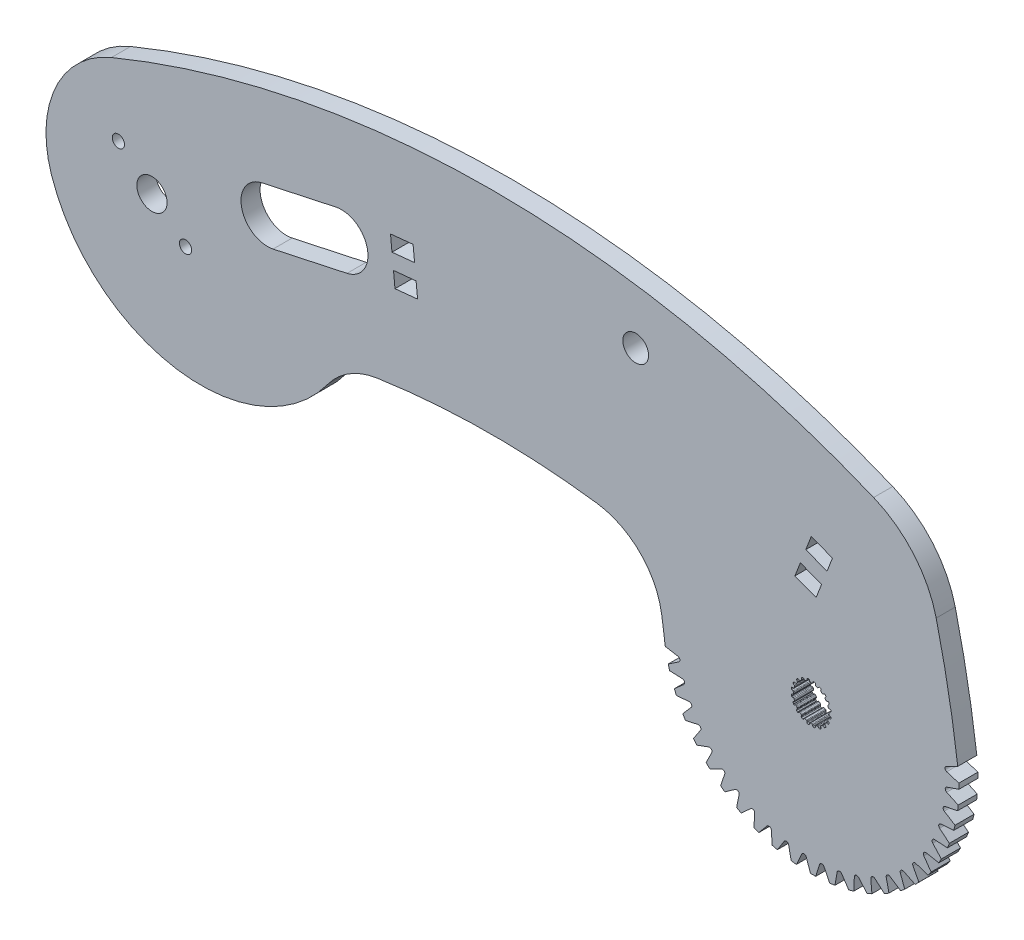
SolidWorks part; units mm, degrees
ref_plane "Front Plane" through (0, 0, 0) normal (0, 0, 1) x (1, 0, 0)
ref_plane "Top Plane" through (0, 0, 0) normal (0, 1, 0) x (1, 0, 0)
ref_plane "Right Plane" through (0, 0, 0) normal (1, 0, 0) x (0, 0, -1)
sketch "Sketch1" plane through (0, 0, 0) normal (0, 0, 1) x (1, 0, 0)
  line L84 (-6.7901, 16.4357) -> (6.7901, -16.4357) construction
  line L85 (121.0901, 16.4357) -> (107.5099, -16.4357) construction
  line L86 (0, 0) -> (114.3, 0) construction
  arc A81 (-6.7901, 16.4357) -> (121.0901, 16.4357) centre (57.15, -138.3341) cw
  arc A82 (6.7901, -16.4357) -> (107.5099, -16.4357) centre (57.15, -138.3341) cw
  arc A84 (-6.7901, 16.4357) -> (6.7901, -16.4357) centre (0, 0) ccw
  arc A85 (121.0901, 16.4357) -> (107.5099, -16.4357) centre (114.3, 0) cw
  dimension "D10" = 131.8914
  dimension "D11" = 35.5662
  dimension "D12" = 114.3
extrude "Boss-Extrude1" add sketch "Sketch1" along normal blind 3.2004
sketch "Sketch3" plane through (0, 0, 3.2004) normal (0, 0, 1) x (1, 0, 0)
  line L0 (114.3, 0) -> (110.6075, -18.6887) construction
  line L5 (83.3792, -7.4554) -> (131.5877, 4.1683)
  line L6 (0, 0) -> (114.3, 0) construction
  line L7 (86.0089, -21.8032) -> (135.2061, -15.5742) construction
  arc A1 (107.5099, -16.4357) -> (121.0901, 16.4357) centre (114.3, 0) ccw construction
  arc A2 (86.0089, -21.8032) -> (135.2061, -15.5742) centre (110.6075, -18.6887) ccw
  arc A3 (83.3792, -7.4554) -> (86.0089, -21.8032) centre (-44.8379, -38.37) cw
  arc A4 (131.5877, 4.1683) -> (135.2061, -15.5742) centre (-44.8379, -38.37) cw
  dimension "D1" = 131.8914
  dimension "D2" = 19.05
  dimension "D3" = 78.823
  dimension "D4" = 49.59
extrude "Boss-Extrude2" add sketch "Sketch3" against normal up to surface (3.2004 mm away) up to face at (57.15, 2.2751, 0)
sketch "Sketch4" plane through (0, 0, 3.2004) normal (0, 0, 1) x (1, 0, 0)
  line L0 (110.5005, -15.7188) -> (110.7144, -15.7188)
  line L1 (110.9234, -15.4512) -> (110.8612, -15.6312)
  line L2 (110.3111, -15.4521) -> (110.3757, -15.6312)
  line L3 (110.3111, -15.4521) -> (110.9234, -15.4512) construction
  line L4 (110.6075, -15.3635) -> (110.6075, -18.6887) construction
  line L5 (110.3757, -15.6312) -> (110.8612, -15.6312) construction
  line L6 (110.1793, -15.3646) -> (111.0356, -15.3624) construction
  line L7 (111.3258, -15.5189) -> (111.3319, -15.7092)
  line L8 (111.4235, -15.8311) -> (111.6269, -15.8972)
  line L9 (111.9084, -15.7073) -> (111.7936, -15.8592)
  line L10 (112.2701, -15.896) -> (112.2171, -16.0789)
  line L11 (112.2666, -16.2232) -> (112.4397, -16.3489)
  line L12 (112.766, -16.2552) -> (112.6099, -16.3642)
  line L13 (113.0518, -16.5464) -> (112.9448, -16.704)
  line L14 (112.9473, -16.8565) -> (113.073, -17.0296)
  line L15 (113.4124, -17.0413) -> (113.2302, -17.0968)
  line L16 (113.5941, -17.4066) -> (113.4438, -17.5234)
  line L17 (113.3989, -17.6693) -> (113.465, -17.8727)
  line L18 (113.7842, -17.9887) -> (113.5938, -17.9852)
  line L19 (113.8441, -18.3923) -> (113.665, -18.4569)
  line L20 (113.5774, -18.5818) -> (113.5774, -18.7957)
  line L21 (113.845, -19.0046) -> (113.665, -18.9424)
  line L22 (113.7773, -19.407) -> (113.587, -19.4131)
  line L23 (113.465, -19.5047) -> (113.3989, -19.7082)
  line L24 (113.5889, -19.9896) -> (113.437, -19.8749)
  line L25 (113.4002, -20.3514) -> (113.2173, -20.2984)
  line L26 (113.073, -20.3478) -> (112.9473, -20.5209)
  line L27 (113.041, -20.8472) -> (112.9319, -20.6912)
  line L28 (112.7497, -21.133) -> (112.5922, -21.0261)
  line L29 (112.4397, -21.0285) -> (112.2666, -21.1543)
  line L30 (112.2549, -21.4936) -> (112.1994, -21.3115)
  line L31 (111.8896, -21.6753) -> (111.7728, -21.525)
  line L32 (111.6269, -21.4802) -> (111.4235, -21.5463)
  line L33 (111.3075, -21.8654) -> (111.311, -21.675)
  line L34 (110.9039, -21.9254) -> (110.8393, -21.7463)
  line L35 (110.7144, -21.6586) -> (110.5005, -21.6586)
  line L36 (110.2916, -21.9262) -> (110.3537, -21.7463)
  line L37 (109.8892, -21.8585) -> (109.8831, -21.6682)
  line L38 (109.7915, -21.5463) -> (109.588, -21.4802)
  line L39 (109.3066, -21.6702) -> (109.4213, -21.5182)
  line L40 (108.9448, -21.4814) -> (108.9978, -21.2986)
  line L41 (108.9484, -21.1543) -> (108.7753, -21.0285)
  line L42 (108.4489, -21.1222) -> (108.605, -21.0132)
  line L43 (108.1632, -20.831) -> (108.2701, -20.6734)
  line L44 (108.2677, -20.5209) -> (108.1419, -20.3478)
  line L45 (107.8026, -20.3361) -> (107.9847, -20.2806)
  line L46 (107.6208, -19.9708) -> (107.7712, -19.854)
  line L47 (107.816, -19.7082) -> (107.7499, -19.5047)
  line L48 (107.4308, -19.3887) -> (107.6212, -19.3922)
  line L49 (107.3708, -18.9851) -> (107.5499, -18.9205)
  line L50 (107.6376, -18.7957) -> (107.6376, -18.5818)
  line L51 (107.37, -18.3728) -> (107.5499, -18.435)
  line L52 (107.4376, -17.9704) -> (107.628, -17.9643)
  line L53 (107.7499, -17.8727) -> (107.816, -17.6693)
  line L54 (107.626, -17.3878) -> (107.778, -17.5026)
  line L55 (107.8147, -17.0261) -> (107.9976, -17.079)
  line L56 (108.1419, -17.0296) -> (108.2677, -16.8565)
  line L57 (108.1739, -16.5302) -> (108.283, -16.6862)
  line L58 (108.4652, -16.2444) -> (108.6228, -16.3513)
  line L59 (108.7753, -16.3489) -> (108.9484, -16.2232)
  line L60 (108.9601, -15.8838) -> (109.0156, -16.066)
  line L61 (109.3254, -15.7021) -> (109.4422, -15.8524)
  line L62 (109.588, -15.8972) -> (109.7915, -15.8311)
  line L63 (109.9075, -15.512) -> (109.904, -15.7024)
  line L64 (111.0356, -15.3624) -> (111.2275, -15.395)
  line L65 (112.0425, -15.6575) -> (112.215, -15.7478)
  line L66 (112.909, -16.2494) -> (113.0451, -16.3884)
  line L67 (113.5501, -17.08) -> (113.6366, -17.2543)
  line L68 (113.9033, -18.068) -> (113.9316, -18.2606)
  line L69 (113.9337, -19.1169) -> (113.9012, -19.3087)
  line L70 (113.6386, -20.1238) -> (113.5484, -20.2962)
  line L71 (113.0468, -20.9902) -> (112.9077, -21.1263)
  line L72 (112.2162, -21.6314) -> (112.0419, -21.7179)
  line L73 (111.2282, -21.9845) -> (111.0356, -22.0129)
  line L74 (110.1793, -22.015) -> (109.9875, -21.9825)
  line L75 (109.1724, -21.7199) -> (109, -21.6297)
  line L76 (108.306, -21.1281) -> (108.1698, -20.989)
  line L77 (107.6648, -20.2975) -> (107.5783, -20.1231)
  line L78 (107.3117, -19.3094) -> (107.2833, -19.1169)
  line L79 (107.2812, -18.2606) -> (107.3137, -18.0687)
  line L80 (107.5763, -17.2536) -> (107.6665, -17.0812)
  line L81 (108.1681, -16.3872) -> (108.3072, -16.2511)
  line L82 (108.9987, -15.746) -> (109.1731, -15.6596)
  line L83 (109.9868, -15.3929) -> (110.1793, -15.3646)
  circle A0 centre (0, 0) radius 2.54
  circle A1 centre (110.6075, -18.6887) radius 3.429 construction
  arc A2 (86.0089, -21.8032) -> (135.2061, -15.5742) centre (110.6075, -18.6887) ccw construction
  arc A3 (-6.7901, 16.4357) -> (6.7901, -16.4357) centre (0, 0) ccw construction
  arc A4 (110.8612, -15.6312) -> (110.7144, -15.7188) centre (110.7358, -15.5878) cw
  arc A5 (110.3757, -15.6312) -> (110.5005, -15.7188) centre (110.5005, -15.5861) ccw
  arc A6 (111.2275, -15.395) -> (111.3258, -15.5189) centre (111.1931, -15.5231) cw
  arc A7 (111.3319, -15.7092) -> (111.4235, -15.8311) centre (111.4645, -15.7049) ccw
  arc A8 (110.1793, -15.3646) -> (110.3111, -15.4521) centre (110.1862, -15.4971) cw
  arc A9 (111.0356, -15.3624) -> (110.9234, -15.4512) centre (111.0488, -15.4945) ccw
  arc A10 (111.7936, -15.8592) -> (111.6269, -15.8972) centre (111.6877, -15.7793) cw
  arc A11 (112.0425, -15.6575) -> (111.9084, -15.7073) centre (112.0143, -15.7872) ccw
  arc A12 (112.215, -15.7478) -> (112.2701, -15.896) centre (112.1427, -15.859) cw
  arc A13 (112.2171, -16.0789) -> (112.2666, -16.2232) centre (112.3446, -16.1158) ccw
  arc A14 (112.6099, -16.3642) -> (112.4397, -16.3489) centre (112.5339, -16.2555) cw
  arc A15 (112.909, -16.2494) -> (112.766, -16.2552) centre (112.842, -16.364) ccw
  arc A16 (113.0451, -16.3884) -> (113.0518, -16.5464) centre (112.9419, -16.4719) cw
  arc A17 (112.9448, -16.704) -> (112.9473, -16.8565) centre (113.0547, -16.7785) ccw
  arc A18 (113.2302, -17.0968) -> (113.073, -17.0296) centre (113.1915, -16.9699) cw
  arc A19 (113.5501, -17.08) -> (113.4124, -17.0413) centre (113.4511, -17.1682) ccw
  arc A20 (113.6366, -17.2543) -> (113.5941, -17.4066) centre (113.5127, -17.3018) cw
  arc A21 (113.4438, -17.5234) -> (113.3989, -17.6693) centre (113.5252, -17.6282) ccw
  arc A22 (113.5938, -17.9852) -> (113.465, -17.8727) centre (113.5962, -17.8525) cw
  arc A23 (113.9033, -18.068) -> (113.7842, -17.9887) centre (113.7817, -18.1214) ccw
  arc A24 (113.9316, -18.2606) -> (113.8441, -18.3923) centre (113.7991, -18.2675) cw
  arc A25 (113.665, -18.4569) -> (113.5774, -18.5818) centre (113.7101, -18.5818) ccw
  arc A26 (113.665, -18.9424) -> (113.5774, -18.7957) centre (113.7083, -18.817) cw
  arc A27 (113.9337, -19.1169) -> (113.845, -19.0046) centre (113.8017, -19.13) ccw
  arc A28 (113.9012, -19.3087) -> (113.7773, -19.407) centre (113.7731, -19.2743) cw
  arc A29 (113.587, -19.4131) -> (113.465, -19.5047) centre (113.5913, -19.5457) ccw
  arc A30 (113.437, -19.8749) -> (113.3989, -19.7082) centre (113.5169, -19.7689) cw
  arc A31 (113.6386, -20.1238) -> (113.5889, -19.9896) centre (113.509, -20.0955) ccw
  arc A32 (113.5484, -20.2962) -> (113.4002, -20.3514) centre (113.4372, -20.2239) cw
  arc A33 (113.2173, -20.2984) -> (113.073, -20.3478) centre (113.1804, -20.4258) ccw
  arc A34 (112.9319, -20.6912) -> (112.9473, -20.5209) centre (113.0407, -20.6151) cw
  arc A35 (113.0468, -20.9902) -> (113.041, -20.8472) centre (112.9322, -20.9233) ccw
  arc A36 (112.9077, -21.1263) -> (112.7497, -21.133) centre (112.8243, -21.0232) cw
  arc A37 (112.5922, -21.0261) -> (112.4397, -21.0285) centre (112.5177, -21.1359) ccw
  arc A38 (112.1994, -21.3115) -> (112.2666, -21.1543) centre (112.3263, -21.2728) cw
  arc A39 (112.2162, -21.6314) -> (112.2549, -21.4936) centre (112.1279, -21.5323) ccw
  arc A40 (112.0419, -21.7179) -> (111.8896, -21.6753) centre (111.9944, -21.5939) cw
  arc A41 (111.7728, -21.525) -> (111.6269, -21.4802) centre (111.6679, -21.6064) ccw
  arc A42 (111.311, -21.675) -> (111.4235, -21.5463) centre (111.4437, -21.6775) cw
  arc A43 (111.2282, -21.9845) -> (111.3075, -21.8654) centre (111.1748, -21.863) ccw
  arc A44 (111.0356, -22.0129) -> (110.9039, -21.9254) centre (111.0287, -21.8803) cw
  arc A45 (110.8393, -21.7463) -> (110.7144, -21.6586) centre (110.7144, -21.7913) ccw
  arc A46 (110.3537, -21.7463) -> (110.5005, -21.6586) centre (110.4792, -21.7896) cw
  arc A47 (110.1793, -22.015) -> (110.2916, -21.9262) centre (110.1661, -21.8829) ccw
  arc A48 (109.9875, -21.9825) -> (109.8892, -21.8585) centre (110.0219, -21.8543) cw
  arc A49 (109.8831, -21.6682) -> (109.7915, -21.5463) centre (109.7504, -21.6725) ccw
  arc A50 (109.4213, -21.5182) -> (109.588, -21.4802) centre (109.5272, -21.5982) cw
  arc A51 (109.1724, -21.7199) -> (109.3066, -21.6702) centre (109.2007, -21.5902) ccw
  arc A52 (109, -21.6297) -> (108.9448, -21.4814) centre (109.0723, -21.5184) cw
  arc A53 (108.9978, -21.2986) -> (108.9484, -21.1543) centre (108.8703, -21.2616) ccw
  arc A54 (108.605, -21.0132) -> (108.7753, -21.0285) centre (108.681, -21.122) cw
  arc A55 (108.306, -21.1281) -> (108.4489, -21.1222) centre (108.3729, -21.0135) ccw
  arc A56 (108.1698, -20.989) -> (108.1632, -20.831) centre (108.273, -20.9055) cw
  arc A57 (108.2701, -20.6734) -> (108.2677, -20.5209) centre (108.1603, -20.5989) ccw
  arc A58 (107.9847, -20.2806) -> (108.1419, -20.3478) centre (108.0234, -20.4076) cw
  arc A59 (107.6648, -20.2975) -> (107.8026, -20.3361) centre (107.7639, -20.2092) ccw
  arc A60 (107.5783, -20.1231) -> (107.6208, -19.9708) centre (107.7023, -20.0756) cw
  arc A61 (107.7712, -19.854) -> (107.816, -19.7082) centre (107.6898, -19.7492) ccw
  arc A62 (107.6212, -19.3922) -> (107.7499, -19.5047) centre (107.6187, -19.5249) cw
  arc A63 (107.3117, -19.3094) -> (107.4308, -19.3887) centre (107.4332, -19.256) ccw
  arc A64 (107.2833, -19.1169) -> (107.3708, -18.9851) centre (107.4159, -19.11) cw
  arc A65 (107.5499, -18.9205) -> (107.6376, -18.7957) centre (107.5049, -18.7957) ccw
  arc A66 (107.5499, -18.435) -> (107.6376, -18.5818) centre (107.5066, -18.5604) cw
  arc A67 (107.2812, -18.2606) -> (107.37, -18.3728) centre (107.4133, -18.2474) ccw
  arc A68 (107.3137, -18.0687) -> (107.4376, -17.9704) centre (107.4419, -18.1031) cw
  arc A69 (107.628, -17.9643) -> (107.7499, -17.8727) centre (107.6237, -17.8317) ccw
  arc A70 (107.778, -17.5026) -> (107.816, -17.6693) centre (107.698, -17.6085) cw
  arc A71 (107.5763, -17.2536) -> (107.626, -17.3878) centre (107.706, -17.2819) ccw
  arc A72 (107.6665, -17.0812) -> (107.8147, -17.0261) centre (107.7778, -17.1535) cw
  arc A73 (107.9976, -17.079) -> (108.1419, -17.0296) centre (108.0346, -16.9516) ccw
  arc A74 (108.283, -16.6862) -> (108.2677, -16.8565) centre (108.1742, -16.7623) cw
  arc A75 (108.1681, -16.3872) -> (108.1739, -16.5302) centre (108.2827, -16.4541) ccw
  arc A76 (108.3072, -16.2511) -> (108.4652, -16.2444) centre (108.3907, -16.3543) cw
  arc A77 (108.6228, -16.3513) -> (108.7753, -16.3489) centre (108.6973, -16.2415) ccw
  arc A78 (109.0156, -16.066) -> (108.9484, -16.2232) centre (108.8886, -16.1046) cw
  arc A79 (108.9987, -15.746) -> (108.9601, -15.8838) centre (109.087, -15.8451) ccw
  arc A80 (109.1731, -15.6596) -> (109.3254, -15.7021) centre (109.2206, -15.7835) cw
  arc A81 (109.4422, -15.8524) -> (109.588, -15.8972) centre (109.547, -15.771) ccw
  arc A82 (109.904, -15.7024) -> (109.7915, -15.8311) centre (109.7713, -15.7) cw
  arc A83 (109.9868, -15.3929) -> (109.9075, -15.512) centre (110.0402, -15.5145) ccw
  circle A84 centre (110.6075, -18.6887) radius 12.7 construction
  point P24 (110.6075, -15.7188)
  dimension "D1" = 6.858
  dimension "D2" = 5.08
  dimension "D5" = 0.1327
  dimension "D10" = 25.4
  dimension "D3" = 0.2139
  dimension "D4" = 0.1904
  dimension "D6" = 0.4855
  dimension "D7" = 0.0877
  dimension "D8" = 0.8563
  dimension "D9" = 2.9699
extrude "Cut-Extrude1" cut sketch "Sketch4" against normal up to surface (3.2004 mm away) up to face at (77.9577, -5.3609, 0)
fillet "Fillet1" radius 12.7 1 edges at (83.7779, -9.1587, 1.6002)
sketch "Sketch7" plane through (0, 0, 3.2004) normal (0, 0, 1) x (1, 0, 0)
  circle A0 centre (110.6075, -18.6887) radius 23.8032 construction
  circle A2 centre (110.6075, -18.6887) radius 12.7 construction
  dimension "D1" = 47.6064
sketch "Sketch8" plane through (0, 0, 3.2004) normal (0, 0, 1) x (1, 0, 0)
  line L0 (-5.6385, 4.8574) -> (5.6385, -4.8574) construction
  line L1 (-6.7901, 16.4357) -> (6.7901, -16.4357) construction
  circle A0 centre (-5.6385, 4.8574) radius 1.025
  circle A1 centre (5.6385, -4.8574) radius 1.025
  circle A4 centre (0, 0) radius 2.54 construction
  point P10 (0, 0)
  dimension "D1" = 2.05
  dimension "D2" = 14.8844
  dimension "D3" = 26.809
extrude "Cut-Extrude3" cut sketch "Sketch8" against normal up to surface (3.2004 mm away) up to face at (77.9593, -6.7182, 0)
sketch "Sketch9" plane through (0, 0, 0) normal (0, 0, -1) x (-1, 0, 0)
  line L0 (-42.0442, 13.129) -> (-42.5483, 8.074) construction
  line L1 (-32.7374, 4.833) -> (-20.3234, 2.1529)
  line L2 (-32.7374, 4.833) -> (-30.8613, 13.5228) construction
  line L3 (-30.8613, 13.5228) -> (-18.4473, 10.8427)
  line L4 (-20.3234, 2.1529) -> (-18.4473, 10.8427) construction
  line L5 (-26.5304, 3.4929) -> (-24.6543, 12.1827) construction
  line L6 (-121.0901, 16.4357) -> (-107.5099, -16.4357) construction
  line L7 (6.7901, 16.4357) -> (-6.7901, -16.4357) construction
  line L8 (-111.9474, 3.6747) -> (-110.1186, -1.0647) construction
  line L9 (-40.4007, 10.4124) -> (-44.1919, 10.7906) construction
  line L10 (-112.8103, 0.6192) -> (-109.2557, 1.9908) construction
  line L11 (-43.9398, 13.318) -> (-40.1486, 12.9399) construction
  line L12 (-43.8138, 14.5817) -> (-40.0226, 14.2036)
  line L13 (-43.8138, 14.5817) -> (-44.0658, 12.0543)
  line L14 (-44.0658, 12.0543) -> (-40.2746, 11.6762)
  line L15 (-40.0226, 14.2036) -> (-40.2746, 11.6762)
  line L20 (-44.4439, 8.2631) -> (-40.6528, 7.885) construction
  line L21 (-44.3179, 9.5268) -> (-40.5267, 9.1487)
  line L22 (-44.3179, 9.5268) -> (-44.57, 6.9994)
  line L23 (-44.57, 6.9994) -> (-40.7788, 6.6213)
  line L24 (-40.5267, 9.1487) -> (-40.7788, 6.6213)
  line L25 (-113.7247, 2.9889) -> (-110.1701, 4.3605) construction
  line L26 (-114.1819, 4.1737) -> (-110.6273, 5.5453)
  line L27 (-114.1819, 4.1737) -> (-113.2675, 1.804)
  line L28 (-113.2675, 1.804) -> (-109.7129, 3.1756)
  line L29 (-110.6273, 5.5453) -> (-109.7129, 3.1756)
  line L30 (-111.8959, -1.7505) -> (-108.3413, -0.3789) construction
  line L31 (-112.3531, -0.5657) -> (-108.7985, 0.8059)
  line L32 (-112.3531, -0.5657) -> (-111.4386, -2.9354)
  line L33 (-111.4386, -2.9354) -> (-107.8841, -1.5638)
  line L34 (-108.7985, 0.8059) -> (-107.8841, -1.5638)
  circle A0 centre (0, 0) radius 2.54 construction
  arc A1 (-114.3, 0) -> (0, 0) centre (-57.15, -138.3341) cw construction
  arc A2 (6.7901, 16.4357) -> (-121.0901, 16.4357) centre (-57.15, -138.3341) ccw construction
  arc A3 (-30.8613, 13.5228) -> (-32.7374, 4.833) centre (-31.7993, 9.1779) ccw
  arc A4 (-18.4473, 10.8427) -> (-20.3234, 2.1529) centre (-19.3853, 6.4978) cw
  point P19 (-31.7993, 9.1779)
  point P20 (-19.3853, 6.4978)
  point P26 (-111.033, 1.305)
  point P27 (-42.2963, 10.6015)
  dimension "D1" = 8.89
  dimension "D2" = 12.7
  dimension "D3" = 20.32
  dimension "D4" = 3.81
  dimension "D5" = 2.54
  dimension "D6" = 3.81
  dimension "D7" = 5.08
extrude "Cut-Extrude4" cut sketch "Sketch9" against normal up to surface (3.2004 mm away) up to face at (-4.6135, 4.8574, 3.2004)
sketch "Sketch10" plane through (0, 0, 0) normal (0, 0, -1) x (-1, 0, 0)
  line L0 (-37.8089, -7.8686) -> (16.8684, -5.63)
  line L1 (0, 0) -> (-114.3, 0) construction
  arc A0 (-37.8089, -7.8686) -> (-29.5382, -12.8633) centre (-39.6449, -20.2538) cw
  arc A1 (-29.5382, -12.8633) -> (16.8684, -5.63) centre (-8.2029, 2.7378) ccw
  arc A2 (-6.7901, -16.4357) -> (-74.6443, -7.6081) centre (-57.15, -138.3341) ccw construction
  arc A3 (-6.7901, -16.4357) -> (6.7901, 16.4357) centre (0, 0) ccw construction
  dimension "D1" = 54.723
  dimension "D2" = 9.6619
  dimension "D3" = 7.8686
extrude "Boss-Extrude3" add sketch "Sketch10" against normal up to surface (3.2004 mm away) up to face at (25.5923, 7.8378, 3.2004)
sketch "Sketch15" plane through (0, 0, 3.2004) normal (0, 0, 1) x (1, 0, 0)
  line L0 (110.6075, -18.6887) -> (135.2983, -16.7468) construction
  line L1 (135.2061, -15.5742) -> (133.2934, -16.5226)
  line L2 (135.3905, -17.9195) -> (133.3531, -17.2818)
  line L3 (135.2061, -15.5742) -> (135.3905, -17.9195) construction
  line L4 (134.2497, -16.0484) -> (134.3718, -17.6006) construction
  line L5 (158.1361, -16.5125) -> (110.6075, -18.6887) construction
  line L6 (135.4022, -18.8116) -> (133.382, -19.5022)
  line L7 (135.2789, -21.1609) -> (133.3421, -20.2627)
  line L8 (135.174, -22.0469) -> (133.081, -22.4679)
  line L9 (134.7452, -24.36) -> (132.9422, -23.2167)
  line L10 (134.5255, -25.2248) -> (132.3955, -25.369)
  line L11 (133.7984, -27.4621) -> (132.1601, -26.0933)
  line L12 (133.4677, -28.2908) -> (131.3371, -28.1557)
  line L13 (132.4549, -30.414) -> (131.0092, -28.8431)
  line L14 (132.0189, -31.1925) -> (129.9241, -30.7805)
  line L15 (130.7375, -33.1654) -> (129.5093, -31.4192)
  line L16 (130.2036, -33.8803) -> (128.1805, -33.1984)
  line L17 (128.6757, -35.669) -> (127.6859, -33.7774)
  line L18 (128.0531, -36.3081) -> (126.1363, -35.368)
  line L19 (126.3047, -37.8821) -> (125.5703, -35.8775)
  line L20 (125.604, -38.4345) -> (123.8264, -37.2522)
  line L21 (123.6652, -39.7668) -> (123.1987, -37.6835)
  line L22 (122.8984, -40.223) -> (121.2902, -38.8188)
  line L23 (120.8022, -41.2909) -> (120.6117, -39.1645)
  line L24 (119.9824, -41.6431) -> (118.5714, -40.041)
  line L25 (117.7648, -42.4282) -> (117.8534, -40.2951)
  line L26 (116.9061, -42.6704) -> (115.7162, -40.8978)
  line L27 (114.605, -43.1593) -> (114.9713, -41.0561)
  line L28 (113.722, -43.2873) -> (112.7736, -41.3746)
  line L29 (111.3767, -43.4718) -> (112.0144, -41.4343)
  line L30 (110.4845, -43.4834) -> (109.794, -41.4633)
  line L31 (108.1353, -43.3602) -> (109.0335, -41.4234)
  line L32 (107.2492, -43.2552) -> (106.8283, -41.1622)
  line L33 (104.9362, -42.8264) -> (106.0795, -41.0234)
  line L34 (104.0714, -42.6067) -> (103.9272, -40.4767)
  line L35 (101.8341, -41.8797) -> (103.2029, -40.2413)
  line L36 (101.0054, -41.549) -> (101.1405, -39.4183)
  line L37 (98.8821, -40.5361) -> (100.4531, -39.0904)
  line L38 (98.1037, -40.1001) -> (98.5157, -38.0053)
  line L39 (96.1308, -38.8187) -> (97.877, -37.5905)
  line L40 (95.4159, -38.2848) -> (96.0978, -36.2617)
  line L41 (93.6271, -36.7569) -> (95.5188, -35.7671)
  line L42 (92.9881, -36.1343) -> (93.9282, -34.2175)
  line L43 (91.414, -34.386) -> (93.4187, -33.6515)
  line L44 (90.8617, -33.6852) -> (92.044, -31.9076)
  line L45 (89.5293, -31.7464) -> (91.6127, -31.2799)
  line L46 (89.0732, -30.9796) -> (90.4774, -29.3715)
  line L47 (88.0053, -28.8835) -> (90.1317, -28.6929)
  line L48 (87.6531, -28.0637) -> (89.2552, -26.6526)
  line L49 (86.868, -25.8461) -> (89.0011, -25.9347)
  line L50 (86.6258, -24.9873) -> (88.3984, -23.7974)
  line L51 (86.1368, -22.6862) -> (88.2401, -23.0525)
  line L52 (86.0089, -21.8032) -> (87.9216, -20.8549) construction
  line L53 (85.8244, -19.458) -> (87.8619, -20.0956) construction
  line L54 (85.8128, -18.5658) -> (87.8329, -17.8752) construction
  line L55 (85.936, -16.2165) -> (87.8728, -17.1147) construction
  line L56 (86.0409, -15.3305) -> (88.134, -14.9095) construction
  line L57 (86.4698, -13.0174) -> (88.2728, -14.1607) construction
  line L58 (86.6895, -12.1526) -> (88.8195, -12.0084) construction
  line L59 (87.4165, -9.9153) -> (89.0549, -11.2842) construction
  line L60 (87.7472, -9.0866) -> (89.8779, -9.2217) construction
  line L61 (88.7601, -6.9634) -> (90.2058, -8.5343) construction
  line L62 (89.1961, -6.1849) -> (91.2909, -6.5969) construction
  line L63 (90.4775, -4.212) -> (91.7057, -5.9582) construction
  line L64 (91.0114, -3.4971) -> (93.0344, -4.1791) construction
  line L65 (92.5393, -1.7084) -> (93.5291, -3.6) construction
  line L66 (93.1619, -1.0693) -> (95.0787, -2.0094) construction
  line L67 (94.9102, 0.5047) -> (95.6447, -1.4999) construction
  line L68 (95.611, 1.0571) -> (97.3886, -0.1252) construction
  line L69 (97.5498, 2.3894) -> (98.0163, 0.3061) construction
  line L70 (98.3166, 2.8456) -> (99.9247, 1.4414) construction
  line L71 (100.4127, 3.9135) -> (100.6033, 1.7871) construction
  line L72 (101.2325, 4.2656) -> (102.6436, 2.6635) construction
  line L73 (103.4501, 5.0508) -> (103.3615, 2.9177) construction
  line L74 (104.3089, 5.2929) -> (105.4988, 3.5204) construction
  line L75 (106.61, 5.7819) -> (106.2437, 3.6787) construction
  line L76 (107.493, 5.9099) -> (108.4413, 3.9972) construction
  line L77 (109.8382, 6.0944) -> (109.2006, 4.0569) construction
  line L78 (110.7304, 6.106) -> (111.421, 4.0858) construction
  line L79 (113.0796, 5.9827) -> (112.1815, 4.0459) construction
  line L80 (113.9657, 5.8778) -> (114.3867, 3.7848) construction
  line L81 (116.2788, 5.449) -> (115.1355, 3.646) construction
  line L82 (117.1436, 5.2293) -> (117.2877, 3.0993) construction
  line L83 (119.3809, 4.5022) -> (118.012, 2.8639) construction
  line L84 (120.2096, 4.1716) -> (120.0745, 2.0409) construction
  line L85 (122.3328, 3.1587) -> (120.7619, 1.713) construction
  line L86 (123.1113, 2.7227) -> (122.6993, 0.6279) construction
  line L87 (125.0842, 1.4413) -> (123.3379, 0.2131) construction
  line L88 (125.7991, 0.9074) -> (125.1171, -1.1157) construction
  line L89 (127.5878, -0.6205) -> (125.6962, -1.6103) construction
  line L90 (128.2269, -1.2431) -> (127.2867, -3.1599) construction
  line L91 (129.8009, -2.9914) -> (127.7963, -3.7259) construction
  line L92 (130.3533, -3.6922) -> (129.171, -5.4698) construction
  line L93 (131.6856, -5.631) -> (129.6023, -6.0975) construction
  line L94 (132.1418, -6.3978) -> (130.7376, -8.0059) construction
  line L95 (133.2097, -8.4939) -> (131.0833, -8.6845) construction
  line L96 (133.5618, -9.3138) -> (131.9597, -10.7248) construction
  line L97 (134.347, -11.5313) -> (132.2139, -11.4427) construction
  line L98 (134.5891, -12.3901) -> (132.8165, -13.58) construction
  line L99 (135.0781, -14.6912) -> (132.9748, -14.3249) construction
  circle A0 centre (110.6075, -18.6887) radius 15.8688 construction
  circle A2 centre (110.6075, -18.6887) radius 24.795 construction
  arc A4 (133.2934, -16.5226) -> (133.3531, -17.2818) centre (133.4756, -16.8902) ccw
  arc A5 (135.2061, -15.5742) -> (135.3905, -17.9195) centre (110.6075, -18.6887) cw
  arc A6 (135.4022, -18.8116) -> (135.2789, -21.1609) centre (110.6075, -18.6887) cw
  arc A7 (133.382, -19.5022) -> (133.3421, -20.2627) centre (133.5147, -19.8905) ccw
  arc A8 (135.174, -22.0469) -> (134.7452, -24.36) centre (110.6075, -18.6887) cw
  arc A9 (133.081, -22.4679) -> (132.9422, -23.2167) centre (133.1619, -22.8702) ccw
  arc A10 (134.5255, -25.2248) -> (133.7984, -27.4621) centre (110.6075, -18.6887) cw
  arc A11 (132.3955, -25.369) -> (132.1601, -26.0933) centre (132.4232, -25.7784) ccw
  arc A12 (133.4677, -28.2908) -> (132.4549, -30.414) centre (110.6075, -18.6887) cw
  arc A13 (131.3371, -28.1557) -> (131.0092, -28.8431) centre (131.3111, -28.5652) ccw
  arc A14 (132.0189, -31.1925) -> (130.7375, -33.1654) centre (110.6075, -18.6887) cw
  arc A15 (129.9241, -30.7805) -> (129.5093, -31.4192) centre (129.8449, -31.1831) ccw
  arc A16 (130.2036, -33.8803) -> (128.6757, -35.669) centre (110.6075, -18.6887) cw
  arc A17 (128.1805, -33.1984) -> (127.6859, -33.7774) centre (128.0495, -33.5872) ccw
  arc A18 (128.0531, -36.3081) -> (126.3047, -37.8821) centre (110.6075, -18.6887) cw
  arc A19 (126.1363, -35.368) -> (125.5703, -35.8775) centre (125.9556, -35.7364) ccw
  arc A20 (125.604, -38.4345) -> (123.6652, -39.7668) centre (110.6075, -18.6887) cw
  arc A21 (123.8264, -37.2522) -> (123.1987, -37.6835) centre (123.5991, -37.5939) ccw
  arc A22 (122.8984, -40.223) -> (120.8022, -41.2909) centre (110.6075, -18.6887) cw
  arc A23 (121.2902, -38.8188) -> (120.6117, -39.1645) centre (121.0204, -39.1279) ccw
  arc A24 (119.9824, -41.6431) -> (117.7648, -42.4282) centre (110.6075, -18.6887) cw
  arc A25 (118.5714, -40.041) -> (117.8534, -40.2951) centre (118.2634, -40.3122) ccw
  arc A26 (116.9061, -42.6704) -> (114.605, -43.1593) centre (110.6075, -18.6887) cw
  arc A27 (115.7162, -40.8978) -> (114.9713, -41.0561) centre (115.3755, -41.1265) ccw
  arc A28 (113.722, -43.2873) -> (111.3767, -43.4718) centre (110.6075, -18.6887) cw
  arc A29 (112.7736, -41.3746) -> (112.0144, -41.4343) centre (112.406, -41.5569) ccw
  arc A30 (110.4845, -43.4834) -> (108.1353, -43.3602) centre (110.6075, -18.6887) cw
  arc A31 (109.794, -41.4633) -> (109.0335, -41.4234) centre (109.4057, -41.596) ccw
  arc A32 (107.2492, -43.2552) -> (104.9362, -42.8264) centre (110.6075, -18.6887) cw
  arc A33 (106.8283, -41.1622) -> (106.0795, -41.0234) centre (106.426, -41.2431) ccw
  arc A34 (104.0714, -42.6067) -> (101.8341, -41.8797) centre (110.6075, -18.6887) cw
  arc A35 (103.9272, -40.4767) -> (103.2029, -40.2413) centre (103.5178, -40.5044) ccw
  arc A36 (101.0054, -41.549) -> (98.8821, -40.5361) centre (110.6075, -18.6887) cw
  arc A37 (101.1405, -39.4183) -> (100.4531, -39.0904) centre (100.731, -39.3924) ccw
  arc A38 (98.1037, -40.1001) -> (96.1308, -38.8187) centre (110.6075, -18.6887) cw
  arc A39 (98.5157, -38.0053) -> (97.877, -37.5905) centre (98.1131, -37.9261) ccw
  arc A40 (95.4159, -38.2848) -> (93.6271, -36.7569) centre (110.6075, -18.6887) cw
  arc A41 (96.0978, -36.2617) -> (95.5188, -35.7671) centre (95.709, -36.1307) ccw
  arc A42 (92.9881, -36.1343) -> (91.414, -34.386) centre (110.6075, -18.6887) cw
  arc A43 (93.9282, -34.2175) -> (93.4187, -33.6515) centre (93.5598, -34.0368) ccw
  arc A44 (90.8617, -33.6852) -> (89.5293, -31.7464) centre (110.6075, -18.6887) cw
  arc A45 (92.044, -31.9076) -> (91.6127, -31.2799) centre (91.7023, -31.6803) ccw
  arc A46 (89.0732, -30.9796) -> (88.0053, -28.8835) centre (110.6075, -18.6887) cw
  arc A47 (90.4774, -29.3715) -> (90.1317, -28.6929) centre (90.1683, -29.1016) ccw
  arc A48 (87.6531, -28.0637) -> (86.868, -25.8461) centre (110.6075, -18.6887) cw
  arc A49 (89.2552, -26.6526) -> (89.0011, -25.9347) centre (88.984, -26.3447) ccw
  arc A50 (86.6258, -24.9873) -> (86.1368, -22.6862) centre (110.6075, -18.6887) cw
  arc A51 (88.3984, -23.7974) -> (88.2401, -23.0525) centre (88.1697, -23.4567) ccw
  arc A52 (86.0089, -21.8032) -> (85.8244, -19.458) centre (110.6075, -18.6887) cw construction
  arc A53 (87.9216, -20.8549) -> (87.8619, -20.0956) centre (87.7393, -20.4872) ccw construction
  arc A54 (85.8128, -18.5658) -> (85.936, -16.2165) centre (110.6075, -18.6887) cw construction
  arc A55 (87.8329, -17.8752) -> (87.8728, -17.1147) centre (87.7002, -17.4869) ccw construction
  arc A56 (86.0409, -15.3305) -> (86.4698, -13.0174) centre (110.6075, -18.6887) cw construction
  arc A57 (88.134, -14.9095) -> (88.2728, -14.1607) centre (88.053, -14.5072) ccw construction
  arc A58 (86.6895, -12.1526) -> (87.4165, -9.9153) centre (110.6075, -18.6887) cw construction
  arc A59 (88.8195, -12.0084) -> (89.0549, -11.2842) centre (88.7918, -11.5991) ccw construction
  arc A60 (87.7472, -9.0866) -> (88.7601, -6.9634) centre (110.6075, -18.6887) cw construction
  arc A61 (89.8779, -9.2217) -> (90.2058, -8.5343) centre (89.9038, -8.8122) ccw construction
  arc A62 (89.1961, -6.1849) -> (90.4775, -4.212) centre (110.6075, -18.6887) cw construction
  arc A63 (91.2909, -6.5969) -> (91.7057, -5.9582) centre (91.3701, -6.1943) ccw construction
  arc A64 (91.0114, -3.4971) -> (92.5393, -1.7084) centre (110.6075, -18.6887) cw construction
  arc A65 (93.0344, -4.1791) -> (93.5291, -3.6) centre (93.1655, -3.7902) ccw construction
  arc A66 (93.1619, -1.0693) -> (94.9102, 0.5047) centre (110.6075, -18.6887) cw construction
  arc A67 (95.0787, -2.0094) -> (95.6447, -1.4999) centre (95.2594, -1.641) ccw construction
  arc A68 (95.611, 1.0571) -> (97.5498, 2.3894) centre (110.6075, -18.6887) cw construction
  arc A69 (97.3886, -0.1252) -> (98.0163, 0.3061) centre (97.6158, 0.2164) ccw construction
  arc A70 (98.3166, 2.8456) -> (100.4127, 3.9135) centre (110.6075, -18.6887) cw construction
  arc A71 (99.9247, 1.4414) -> (100.6033, 1.7871) centre (100.1946, 1.7505) ccw construction
  arc A72 (101.2325, 4.2656) -> (103.4501, 5.0508) centre (110.6075, -18.6887) cw construction
  arc A73 (102.6436, 2.6635) -> (103.3615, 2.9177) centre (102.9515, 2.9347) ccw construction
  arc A74 (104.3089, 5.2929) -> (106.61, 5.7819) centre (110.6075, -18.6887) cw construction
  arc A75 (105.4988, 3.5204) -> (106.2437, 3.6787) centre (105.8395, 3.7491) ccw construction
  arc A76 (107.493, 5.9099) -> (109.8382, 6.0944) centre (110.6075, -18.6887) cw construction
  arc A77 (108.4413, 3.9972) -> (109.2006, 4.0569) centre (108.809, 4.1794) ccw construction
  arc A78 (110.7304, 6.106) -> (113.0796, 5.9827) centre (110.6075, -18.6887) cw construction
  arc A79 (111.421, 4.0858) -> (112.1815, 4.0459) centre (111.8092, 4.2186) ccw construction
  arc A80 (113.9657, 5.8778) -> (116.2788, 5.449) centre (110.6075, -18.6887) cw construction
  arc A81 (114.3867, 3.7848) -> (115.1355, 3.646) centre (114.789, 3.8657) ccw construction
  arc A82 (117.1436, 5.2293) -> (119.3809, 4.5022) centre (110.6075, -18.6887) cw construction
  arc A83 (117.2877, 3.0993) -> (118.012, 2.8639) centre (117.6971, 3.127) ccw construction
  arc A84 (120.2096, 4.1716) -> (122.3328, 3.1587) centre (110.6075, -18.6887) cw construction
  arc A85 (120.0745, 2.0409) -> (120.7619, 1.713) centre (120.484, 2.015) ccw construction
  arc A86 (123.1113, 2.7227) -> (125.0842, 1.4413) centre (110.6075, -18.6887) cw construction
  arc A87 (122.6993, 0.6279) -> (123.3379, 0.2131) centre (123.1019, 0.5487) ccw construction
  arc A88 (125.7991, 0.9074) -> (127.5878, -0.6205) centre (110.6075, -18.6887) cw construction
  arc A89 (125.1171, -1.1157) -> (125.6962, -1.6103) centre (125.506, -1.2467) ccw construction
  arc A90 (128.2269, -1.2431) -> (129.8009, -2.9914) centre (110.6075, -18.6887) cw construction
  arc A91 (127.2867, -3.1599) -> (127.7963, -3.7259) centre (127.6551, -3.3406) ccw construction
  arc A92 (130.3533, -3.6922) -> (131.6856, -5.631) centre (110.6075, -18.6887) cw construction
  arc A93 (129.171, -5.4698) -> (129.6023, -6.0975) centre (129.5126, -5.6971) ccw construction
  arc A94 (132.1418, -6.3978) -> (133.2097, -8.4939) centre (110.6075, -18.6887) cw construction
  arc A95 (130.7376, -8.0059) -> (131.0833, -8.6845) centre (131.0466, -8.2758) ccw construction
  arc A96 (133.5618, -9.3138) -> (134.347, -11.5313) centre (110.6075, -18.6887) cw construction
  arc A97 (131.9597, -10.7248) -> (132.2139, -11.4427) centre (132.2309, -11.0328) ccw construction
  arc A98 (134.5891, -12.3901) -> (135.0781, -14.6912) centre (110.6075, -18.6887) cw construction
  arc A99 (132.8165, -13.58) -> (132.9748, -14.3249) centre (133.0452, -13.9207) ccw construction
  circle A101 centre (110.6075, -18.6887) radius 12.7 construction
  point P16 (134.3108, -16.8245)
  point P43 (110.6075, -18.6887)
  dimension "D1" = 31.7376
  dimension "D6" = 49.59
  dimension "D2" = 0.9906
  dimension "D3" = 1.557
  dimension "D4" = 20
  dimension "D5" = 48
extrude "Cut-Extrude5" cut sketch "Sketch15" against normal up to surface (3.2004 mm away) up to face at (67.7321, -7.1382, 0)
sketch "Sketch16" plane through (0, 0, 0) normal (0, 0, -1) x (-1, 0, 0)
  line L0 (-81.1715, 18.1918) -> (-81.1715, 0) construction
  line L2 (0, 0) -> (-114.3, 0) construction
  circle A0 centre (-81.1715, 18.1918) radius 2.159
  point P4 (0, 0)
  dimension "D1" = 4.318
  dimension "D2" = 18.1918
  dimension "D3" = 33.1285
extrude "Cut-Extrude6" cut sketch "Sketch16" against normal up to surface (3.2004 mm away) up to face at (25.5923, 7.8378, 3.2004)
